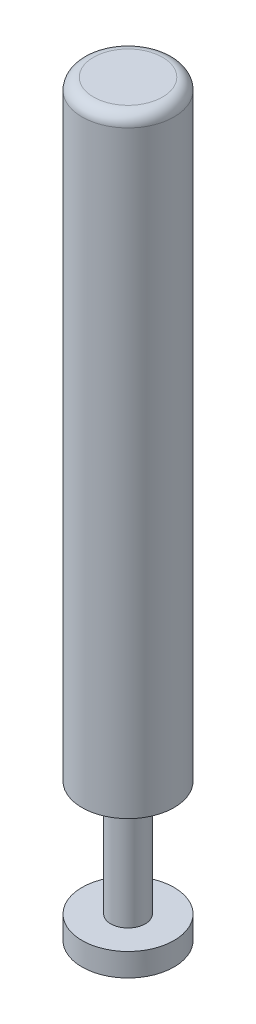
SolidWorks part; units mm, degrees
material "1023 炭素鋼板 (SS)"
ref_plane "Front" through (0, 0, 0) normal (0, 0, 1) x (1, 0, 0)
ref_plane "Top" through (0, 0, 0) normal (0, 1, 0) x (1, 0, 0)
ref_plane "Right" through (0, 0, 0) normal (1, 0, 0) x (0, 0, -1)
sketch "ｽｹｯﾁ1" plane through (0, 0, 0) normal (0, 1, 0) x (1, 0, 0)
  circle A0 centre (0, 0) radius 2
  dimension "D1" = 4
extrude "ﾎﾞｽ - 押し出し1" add sketch "ｽｹｯﾁ1" along normal blind 32.5
sketch "ｽｹｯﾁ2" plane through (0, 0, 0) normal (0, -1, 0) x (1, 0, 0)
  circle A0 centre (0, 0) radius 0.75
  circle A2 centre (0, 0) radius 2
  circle A3 centre (0, 0) radius 2
  circle M2 centre (0, 0) radius 2
  dimension "D1" = 1.5
  dimension "D2" = 0
extrude "ｶｯﾄ - 押し出し1" cut sketch "ｽｹｯﾁ2" against normal blind 5 from offset 1 contours A0 M2 offset against normal yes
fillet "ﾌｨﾚｯﾄ1" radius 0.5 1 edges at (0, 32.5, 2)
